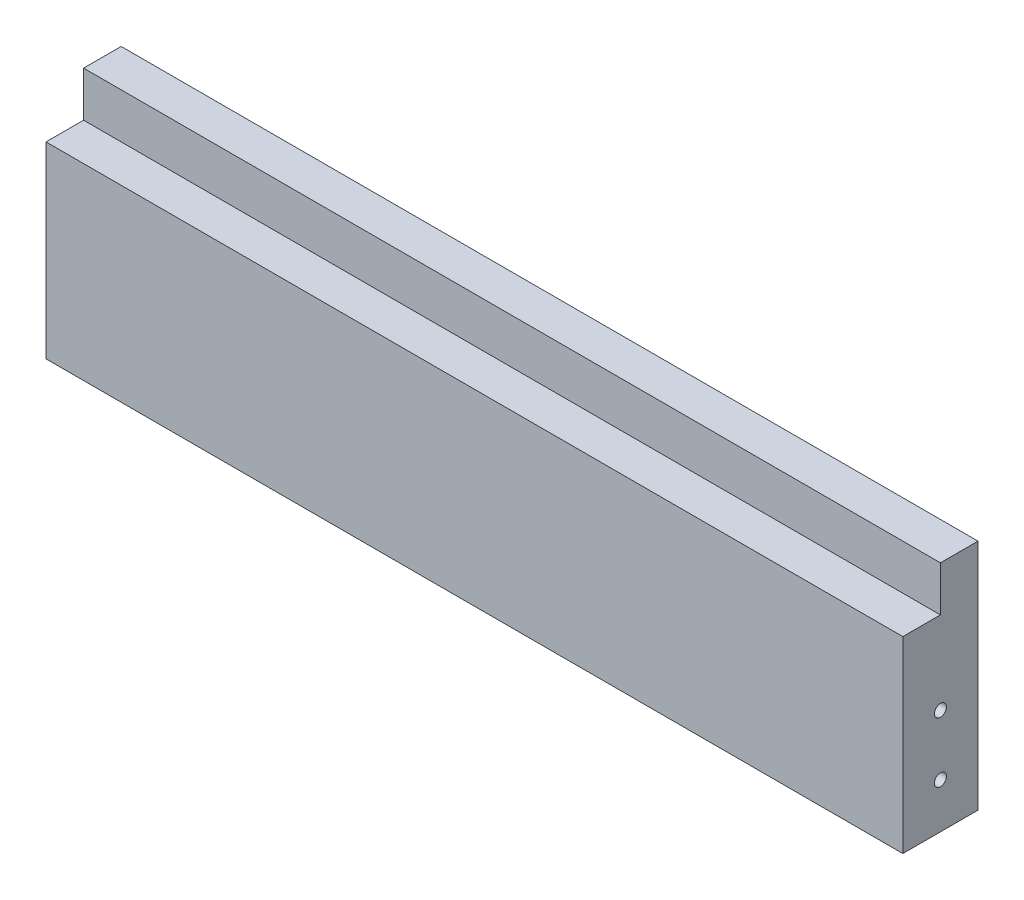
SolidWorks part; units mm, degrees
ref_plane "正面" through (0, 0, 0) normal (0, 0, 1) x (1, 0, 0)
ref_plane "平面" through (0, 0, 0) normal (0, 1, 0) x (1, 0, 0)
ref_plane "右側面" through (0, 0, 0) normal (1, 0, 0) x (0, 0, -1)
sketch "Sketch1" plane through (0, 0, 0) normal (0, 0, 1) x (1, 0, 0)
  line L1 (0, 0) -> (114, 0)
  line L2 (0, 0) -> (0, 31)
  line L3 (0, 31) -> (114, 31)
  line L4 (114, 0) -> (114, 31)
extrude "Boss-Extrude1" add sketch "Sketch1" along normal blind 10
sketch "Sketch2" plane through (0, 0, 10) normal (0, 0, 1) x (1, 0, 0)
  line L0 (0, 31) -> (0, 0) construction
  line L1 (114, 31) -> (0, 31)
  line L2 (114, 31) -> (114, 25)
  line L3 (114, 25) -> (0, 25)
  line L4 (0, 31) -> (0, 25)
extrude "Cut-Extrude1" cut sketch "Sketch2" against normal blind 5
hole_wizard "M2x0.4 Tapped Hole1" positions "3DSketch1" profile "Sketch3" tap size "M2x0.4" standard "JIS"
sketch3d "3DSketch1"
  line L0 (0, 31, 0) -> (0, 0, 0) construction
  line L1 (0, 0, 10) -> (0, 0, 0) construction
  point P0 (0, 14, 5)
  point P2 (0, 6, 5)
  dimension "D1" = 5
  dimension "D2" = 5
  dimension "D3" = 6
  dimension "D4" = 14
sketch "Sketch3" plane through (0, 14, 5) normal (0, 1, 0) x (0, 0, 1)
  line L0 (0, 0) -> (0, 7.4807)
  line L1 (0, 7.4807) -> (0.8, 7)
  line L2 (0.8, 7) -> (0.8, 0)
  line L5 (0.8, 0) -> (0, 0)
  line L10 (0, 7.4807) -> (-0.8, 7) construction
  line L11 (0, -6.35) -> (0, 107.95) construction
  dimension "Tap Drill Dia." = 1.6
  dimension "Tap Drill Depth" = 7
  dimension "Drill Angle" = 118
cosmetic thread "Hole Thread1"
cosmetic thread "Hole Thread2"
hole_wizard "M2x0.4 Tapped Hole3" positions "3DSketch2" profile "Sketch4" tap size "M2x0.4" standard "JIS"
sketch3d "3DSketch2"
  line L0 (114, 0, 10) -> (114, 25, 10) construction
  line L1 (114, 0, 10) -> (114, 0, 0) construction
  point P0 (114, 14, 5)
  point P2 (114, 6, 5)
  dimension "D1" = 5
  dimension "D2" = 14
  dimension "D3" = 5
  dimension "D4" = 6
sketch "Sketch4" plane through (114, 14, 5) normal (0, 1, 0) x (0, 0, -1)
  line L0 (0, 0) -> (0, 7.4807)
  line L1 (0, 7.4807) -> (0.8, 7)
  line L2 (0.8, 7) -> (0.8, 0)
  line L5 (0.8, 0) -> (0, 0)
  line L10 (0, 7.4807) -> (-0.8, 7) construction
  line L11 (0, -6.35) -> (0, 107.95) construction
  dimension "Tap Drill Dia." = 1.6
  dimension "Tap Drill Depth" = 7
  dimension "Drill Angle" = 118
cosmetic thread "Hole Thread3"
cosmetic thread "Hole Thread4"
hole_wizard "M2x0.4 Tapped Hole2" positions "Sketch6" profile "Sketch5" tap size "M2x0.4" standard "JIS"
sketch "Sketch6" plane through (0, 0, 0) normal (0, -1, 0) x (-1, 0, 0)
  line L1 (-114, -10) -> (-114, 0) construction
  line L2 (0, -10) -> (0, 0) construction
  point P0 (-102, -5)
  point P1 (-12, -5)
  point P3 (-57, -5)
  point P5 (-79, -5)
  point P7 (-35, -5)
  dimension "D1" = 12
  dimension "D2" = 35
  dimension "D3" = 12
  dimension "D4" = 35
cosmetic thread "Hole Thread5"
sketch "Sketch5" plane through (102, 0, 5) normal (1, 0, 0) x (0, 0, -1)
  line L0 (0, 0) -> (0, 7.4807)
  line L1 (0, 7.4807) -> (0.8, 7)
  line L2 (0.8, 7) -> (0.8, 0)
  line L5 (0.8, 0) -> (0, 0)
  line L10 (0, 7.4807) -> (-0.8, 7) construction
  line L11 (0, -6.35) -> (0, 107.95) construction
  dimension "Tap Drill Dia." = 1.6
  dimension "Tap Drill Depth" = 7
  dimension "Drill Angle" = 118
cosmetic thread "Hole Thread6"
cosmetic thread "Hole Thread7"
cosmetic thread "Hole Thread8"
cosmetic thread "Hole Thread9"
